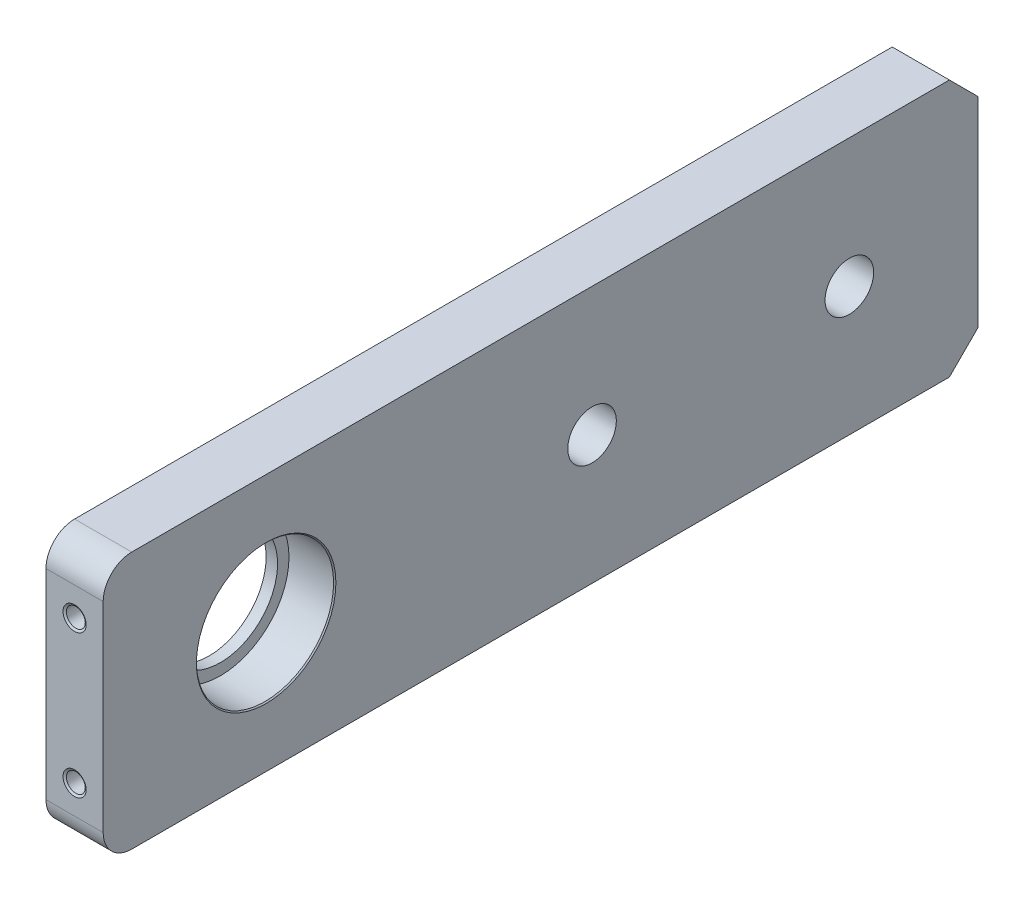
SolidWorks part; units mm, degrees
material "6061 合金"
ref_plane "前视基准面" through (0, 0, 0) normal (0, 0, 1) x (1, 0, 0)
ref_plane "上视基准面" through (0, 0, 0) normal (0, 1, 0) x (1, 0, 0)
ref_plane "右视基准面" through (0, 0, 0) normal (1, 0, 0) x (0, 0, -1)
sketch "草图1" plane through (0, 0, 0) normal (1, 0, 0) x (0, 0, -1)
  line L0 (108, 5.3536) -> (108, -59.1865) construction
  line L1 (0, 0) -> (153, 0)
  line L2 (0, 0) -> (0, -45)
  line L3 (0, -45) -> (153, -45)
  line L4 (153, 0) -> (153, -45)
  circle A0 centre (28.5, -22.5) radius 10
  circle A1 centre (85.5, -22.5) radius 4.25
  circle A2 centre (130.5, -22.5) radius 4.25
  dimension "D3" = 28.5
  dimension "D4" = 20
  dimension "D5" = 22.5
  dimension "D6" = 8.5
  dimension "D7" = 45
  dimension "D8" = 45
  dimension "D9" = 8.5
  dimension "D1" = 45
  dimension "D2" = 153
extrude "凸台-拉伸1" add sketch "草图1" along normal mid plane 10
sketch "草图6" plane through (5, 0, 0) normal (-1, 0, 0) x (0, 0, 1)
  circle A0 centre (-28.5, -22.5) radius 12
  dimension "D1" = 24
extrude "轴承孔" cut sketch "草图6" along normal blind 8
chamfer "倒角1" distance 5 angle 45 2 edges at (0, -45, -153) (0, 0, -153)
fillet "圆角1" radius 5 2 edges at (0, 0, 0) (0, -45, 0)
chamfer "倒角2" distance 0.2 angle 45 1 edges at (5, -22.5, -16.5)
hole_wizard "M4 螺纹孔1" positions "草图8" profile "草图7" tap size "M4" standard "GB"
sketch "草图8" plane through (0, 0, 0) normal (0, 0, 1) x (1, 0, 0)
  line L0 (5, -22.5) -> (-10.3008, -22.5) construction
  line L1 (5, -5) -> (5, -40) construction
  line L3 (0, 0) -> (0, -47.9281) construction
  point P0 (0, -10)
  point P2 (0, -35)
  dimension "D1" = 25
sketch "草图7" plane through (0, -10, 0) normal (1, 0, 0) x (0, -1, 0)
  line L0 (0, 0) -> (0, 15.5)
  line L1 (0, 15.5) -> (1.65, 15.5)
  line L2 (1.65, 15.5) -> (1.65, 0.2165)
  line L3 (1.65, 0.2165) -> (2.025, 0)
  line L5 (2.025, 0) -> (0, 0)
  line L6 (-1.65, 0.2165) -> (-2.025, 0) construction
  line L10 (0, 15.5) -> (-1.65, 15.5) construction
  line L11 (0, -6.35) -> (0, 107.95) construction
  dimension "螺纹孔钻头直径" = 3.3
  dimension "螺纹孔钻头深度" = 15.5
  dimension "近端锥形沉头孔直径" = 4.05
  dimension "近端锥形沉头孔角度" = 120
  dimension "导头角度" = 180
cosmetic thread "孔螺蚊线1" parameters "D1"=12, "D2"=4
cosmetic thread "孔螺蚊线3" parameters "D1"=12, "D2"=4
